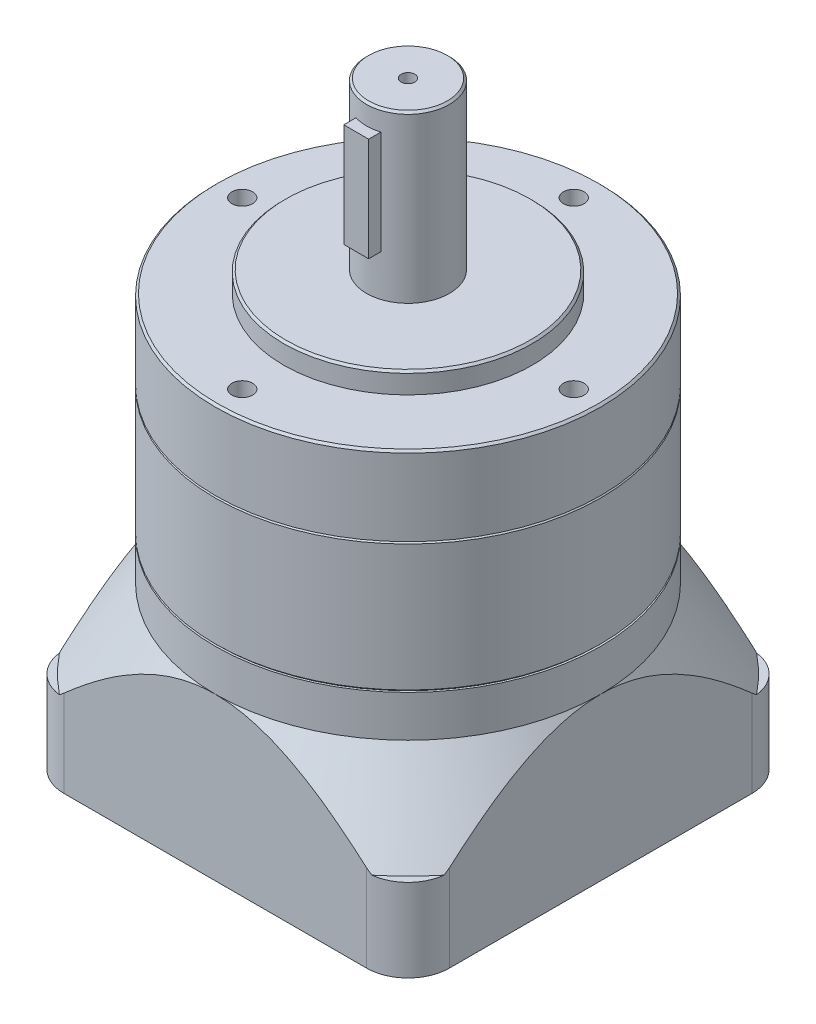
SolidWorks part; units mm, degrees
ref_plane "前基準面" through (0, 0, 0) normal (0, 0, 1) x (1, 0, 0)
ref_plane "上基準面" through (0, 0, 0) normal (0, 1, 0) x (1, 0, 0)
ref_plane "右基準面" through (0, 0, 0) normal (1, 0, 0) x (0, 0, -1)
sketch "草圖1" plane through (0, 0, 0) normal (0, 1, 0) x (1, 0, 0)
  line L1 (-36.5, -46.5) -> (36.5, -46.5)
  line L2 (-46.5, -36.5) -> (-46.5, 36.5)
  line L3 (-36.5, 46.5) -> (36.5, 46.5)
  line L4 (46.5, -36.5) -> (46.5, 36.5)
  line L5 (-46.5, -46.5) -> (46.5, 46.5) construction
  line L6 (-46.5, 46.5) -> (46.5, -46.5) construction
  arc A0 (36.5, -46.5) -> (46.5, -36.5) centre (36.5, -36.5) ccw
  arc A1 (-36.5, -46.5) -> (-46.5, -36.5) centre (-36.5, -36.5) cw
  arc A2 (36.5, 46.5) -> (46.5, 36.5) centre (36.5, 36.5) cw
  arc A3 (-46.5, 36.5) -> (-36.5, 46.5) centre (-36.5, 36.5) cw
  point P0 (0, 0)
  dimension "D3" = 10
  dimension "D1" = 93
  dimension "D2" = 93
extrude "填料-伸長1" add sketch "草圖1" along normal blind 49
sketch "草圖2" plane through (0, 49, 0) normal (0, 1, 0) x (1, 0, 0)
  circle A0 centre (0, 0) radius 46.5
extrude "除料-伸長3" cut sketch "草圖2" along normal blind 10 and the other way blind 19 draft 35 from offset 10 flip side to cut offset against normal yes
sketch "草圖3" plane through (0, 49, 0) normal (0, 1, 0) x (1, 0, 0)
  circle A0 centre (0, 0) radius 46.5
extrude "填料-伸長2" add sketch "草圖3" along normal blind 31.5 separate body
sketch "草圖4" plane through (0, 80.5, 0) normal (0, 1, 0) x (1, 0, 0)
  circle A0 centre (0, 0) radius 46.5
extrude "填料-伸長3" add sketch "草圖4" along normal blind 19 separate body
chamfer "導角1" distance 0.5 angle 45 2 edges at (0, 80.5, 46.5) (0, 49, 46.5)
sketch "草圖6" plane through (0, 99.5, 0) normal (0, 1, 0) x (1, 0, 0)
  circle A0 centre (0, 0) radius 30
  dimension "D1" = 60
extrude "填料-伸長5" add sketch "草圖6" along normal blind 5
sketch "草圖7" plane through (0, 104.5, 0) normal (0, 1, 0) x (1, 0, 0)
  circle A0 centre (0, 0) radius 10
  dimension "D1" = 20
extrude "填料-伸長6" add sketch "草圖7" along normal blind 40
chamfer "導角2" distance 0.5 angle 45 3 edges at (0, 144.5, 10) (0, 99.5, 46.5) (0, 104.5, 30)
hole_wizard "M6x1.0 螺紋孔1" positions "草圖9" profile "草圖8" tap size "M6x1.0" standard "JIS"
sketch "草圖9" plane through (0, 99.5, 0) normal (0, 1, 0) x (1, 0, 0)
  point P0 (0, 40)
sketch "草圖8" plane through (0, 99.5, -40) normal (1, 0, 0) x (0, 0, 1)
  line L0 (0, 0) -> (0, 16.5022)
  line L1 (0, 16.5022) -> (2.5, 15)
  line L2 (2.5, 15) -> (2.5, 0)
  line L5 (2.5, 0) -> (0, 0)
  line L10 (0, 16.5022) -> (-2.5, 15) construction
  line L11 (0, -6.35) -> (0, 107.95) construction
  dimension "螺孔鑽直徑" = 5
  dimension "螺孔鑽深度" = 15
  dimension "導頭角度" = 118
cosmetic thread "鑽孔螺紋1" parameters "D1"=12, "D2"=6
pattern_circular "環狀複製排列1" count 4 over 360 about axis through (0, 0, 0) along (0, 1, 0) of "M6x1.0 螺紋孔1"
sketch "草圖10" plane through (0, 0, 0) normal (0, 0, 1) x (1, 0, 0)
  line L0 (9.5, 144.5) -> (-9.5, 144.5) construction
  line L1 (-3, 139.5) -> (3, 139.5)
  line L2 (-3, 139.5) -> (-3, 114.5)
  line L3 (-3, 114.5) -> (3, 114.5)
  line L4 (3, 139.5) -> (3, 114.5)
  line L5 (0, -51.15) -> (0, 51.15) construction
  dimension "D1" = 5
  dimension "D2" = 6
  dimension "D3" = 3
  dimension "D4" = 25
extrude "填料-伸長7" add sketch "草圖10" along normal blind 12.5
sketch "草圖11" plane through (0, 0, 0) normal (0, -1, 0) x (1, 0, 0)
  circle A0 centre (0, 0) radius 35
  dimension "D1" = 70
extrude "除料-伸長4" cut sketch "草圖11" against normal blind 6
sketch "草圖12" plane through (0, 6, 0) normal (0, -1, 0) x (1, 0, 0)
  circle A0 centre (0, 0) radius 10
  dimension "D1" = 20
extrude "除料-伸長5" cut sketch "草圖12" against normal blind 40
hole_wizard "M4x0.7 螺紋孔1" positions "草圖14" profile "草圖13" tap size "M4x0.7" standard "JIS"
sketch "草圖14" plane through (0, 144.5, 0) normal (0, 1, 0) x (1, 0, 0)
  point P0 (0, 0)
sketch "草圖13" plane through (0, 144.5, 0) normal (1, 0, 0) x (0, 0, 1)
  line L0 (0, 0) -> (0, 11.0914)
  line L1 (0, 11.0914) -> (1.65, 10.1)
  line L2 (1.65, 10.1) -> (1.65, 0)
  line L5 (1.65, 0) -> (0, 0)
  line L10 (0, 11.0914) -> (-1.65, 10.1) construction
  line L11 (0, -6.35) -> (0, 107.95) construction
  dimension "螺孔鑽直徑" = 3.3
  dimension "螺孔鑽深度" = 10.1
  dimension "導頭角度" = 118
cosmetic thread "鑽孔螺紋2" parameters "D1"=8, "D2"=4
